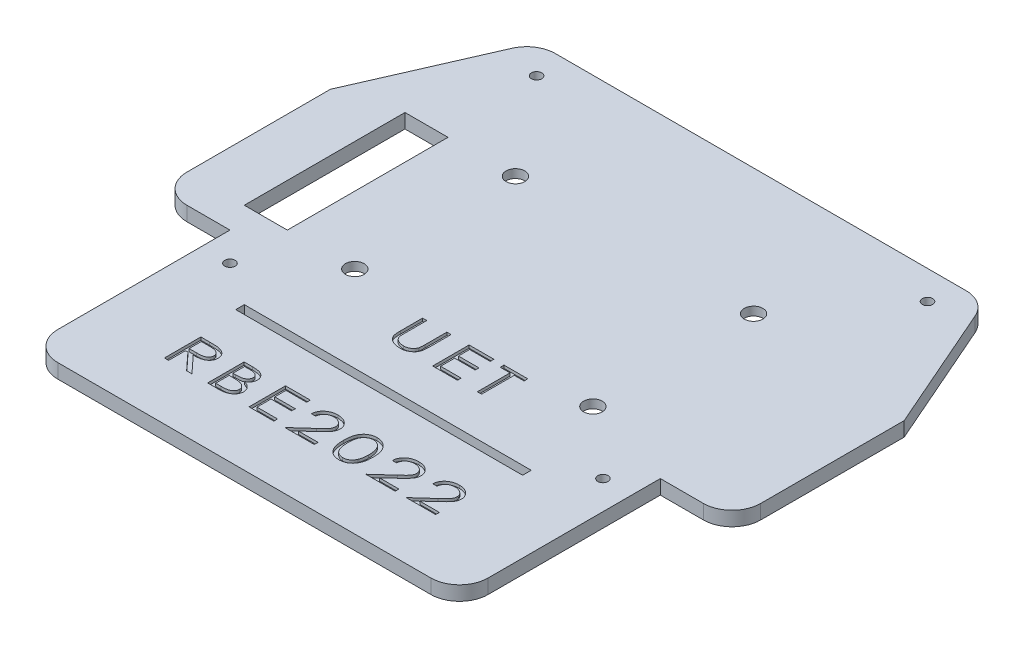
SolidWorks part; units mm, degrees
ref_plane "Front Plane" through (0, 0, 0) normal (0, 0, 1) x (1, 0, 0)
ref_plane "Top Plane" through (0, 0, 0) normal (0, 1, 0) x (1, 0, 0)
ref_plane "Right Plane" through (0, 0, 0) normal (1, 0, 0) x (0, 0, -1)
sketch "Sketch1" plane through (0, 0, 0) normal (0, 1, 0) x (1, 0, 0)
  line L13 (-100, -40) -> (-100, 10)
  line L17 (75, -60) -> (75, -50)
  line L18 (75, -50) -> (90, -50)
  line L19 (-75, -60) -> (-75, -50)
  line L20 (-75, -50) -> (-90, -50)
  line L31 (-75, -60) -> (-75, -110)
  line L32 (-65, -120) -> (65, -120)
  line L33 (75, -110) -> (75, -60)
  line L34 (-75, -60) -> (-65, -60) construction
  line L35 (0, -55) -> (0, 55) construction
  line L38 (-100, 10) -> (100, 10) construction
  line L39 (100, -40) -> (100, 10)
  line L40 (100, 10) -> (78.125, 60)
  line L42 (-78.125, 60) -> (-100, 10)
  line L44 (-78.125, 60) -> (78.125, 60)
  arc A6 (90, -50) -> (100, -40) centre (90, -40) ccw
  arc A7 (-90, -50) -> (-100, -40) centre (-90, -40) cw
  arc A8 (65, -120) -> (75, -110) centre (65, -110) ccw
  arc A9 (-75, -110) -> (-65, -120) centre (-65, -110) ccw
  circle A10 centre (-65, -60) radius 1.8
  circle A11 centre (65, -60) radius 1.8
  point P9 (-75, -70)
  point P15 (95, -70)
  point P16 (70, -70)
  point P21 (0, -70)
  point P22 (75, -120)
  point P24 (-100, -70)
  point P26 (-75, -120)
  dimension "D6" = 10
  dimension "D3" = 70
  dimension "D8" = 3.6
  dimension "D1" = 156.25
  dimension "D2" = 50
  dimension "D4" = 25
  dimension "D5" = 150
  dimension "D7" = 10
  dimension "D9" = 50
  dimension "D10" = 25
extrude "Boss-Extrude1" add sketch "Sketch1" along normal blind 5
sketch "Sketch8" plane through (0, 5, 0) normal (0, 1, 0) x (1, 0, 0)
  line L0 (-75, -50) -> (75, -50) construction
  line L1 (0, -50) -> (0, -71.5) construction
  line L3 (-50, -70) -> (50, -70)
  line L4 (-75, -50) -> (-75, -70) construction
  line L5 (-75, -50) -> (-75, -110) construction
  line L6 (-50, -70) -> (-50, -73)
  line L7 (-50, -73) -> (50, -73)
  line L8 (50, -70) -> (50, -73)
  line L9 (-50, -70) -> (50, -73) construction
  line L10 (-50, -73) -> (50, -70) construction
  dimension "D2" = 3
  dimension "D3" = 100
  dimension "D1" = 21.5
extrude "Cut-Extrude5" cut sketch "Sketch8" against normal blind 10
sketch "Sketch9" plane through (0, 5, 0) normal (0, 1, 0) x (1, 0, 0)
  line L0 (-75, -50) -> (75, -50) construction
  line L1 (0, -40) -> (-80, -40) construction
  line L2 (0, -40) -> (0, 16) construction
  line L3 (0, 16) -> (41.5, 16) construction
  line L4 (0, -40) -> (41.5, -40) construction
  line L5 (-78.125, 60) -> (-78.125, 50) construction
  line L6 (0, -55) -> (0, 55) construction
  line L7 (-78.125, 50) -> (-68.125, 50) construction
  line L8 (0, -40) -> (0, -50) construction
  line L9 (-80, -40) -> (-65, -40)
  line L10 (-80, -40) -> (-80, 16)
  line L11 (-80, 16) -> (-65, 16)
  line L12 (-65, -40) -> (-65, 16)
  circle A10 centre (-68.125, 50) radius 1.8
  circle A11 centre (68.125, 50) radius 1.8
  circle A12 centre (41.5, 16) radius 3.25
  circle A13 centre (41.5, -40) radius 3.25
  circle A14 centre (-41.5, 16) radius 3.25
  circle A15 centre (-41.5, -40) radius 3.25
  dimension "D2" = 10
  dimension "D4" = 10
  dimension "D5" = 41.5
  dimension "D6" = 41.5
  dimension "D7" = 6.5
  dimension "D8" = 3.6
  dimension "D9" = 6.5
  dimension "D10" = 15
  dimension "D1" = 80
  dimension "D3" = 56
  dimension "D11" = 10
extrude "Cut-Extrude6" cut sketch "Sketch9" against normal blind 10
sketch "Sketch10" plane through (0, 5, 0) normal (0, 1, 0) x (1, 0, 0)
  line L3 (-100, 10) -> (100, 10) construction
  line L6 (0, 10) -> (0, -120) construction
  line L8 (-65, -120) -> (65, -120) construction
  line L10 (-35, -12) -> (0, -12) construction
sketch "Sketch12" plane through (0, 0, 0) normal (1, 0, 0) x (0, 0, -1)
  line L0 (-12, 5) -> (-12, 24) construction
  dimension "D1" = 19
ref_point "cartpendulum"
fillet "Fillet1" radius 10 2 edges at (78.125, 2.5, -60) (-78.125, 2.5, -60)
sketch "Sketch13" plane through (0, 5, 0) normal (0, 1, 0) x (1, 0, 0)
  text T0 "    UET\r\n\r\nRBE2022" font "Century Gothic" height in points 48
extrude "Cut-Extrude7" cut sketch "Sketch13" against normal blind 1
sketch "Sketch14" plane through (0, 0, 0) normal (0, -1, 0) x (1, 0, 0)
  circle A0 centre (-41.5, 40) radius 7.5
  circle A1 centre (41.5, 40) radius 7.5
  circle A2 centre (41.5, -16) radius 7.5
  circle A3 centre (-41.5, -16) radius 7.5
  dimension "D1" = 15
  dimension "D2" = 15
  dimension "D3" = 15
  dimension "D4" = 15
extrude "Cut-Extrude8" cut sketch "Sketch14" against normal blind 2
